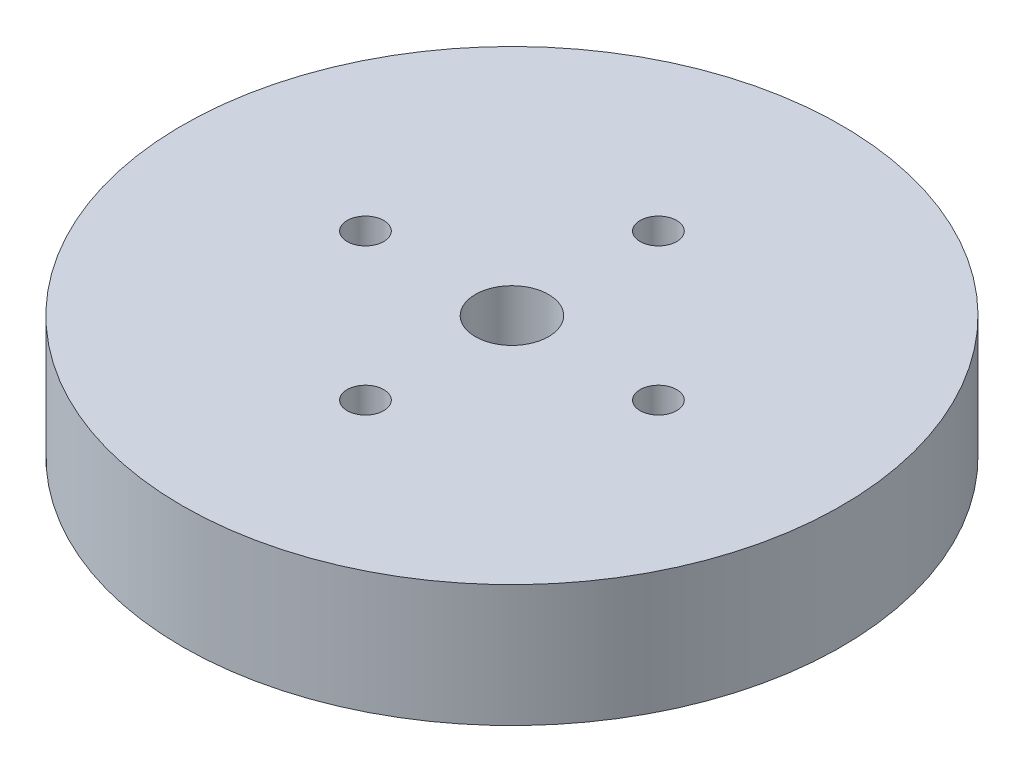
SolidWorks part; units mm, degrees
ref_plane "Front Plane" through (0, 0, 0) normal (0, 0, 1) x (1, 0, 0)
ref_plane "Top Plane" through (0, 0, 0) normal (0, 1, 0) x (1, 0, 0)
ref_plane "Right Plane" through (0, 0, 0) normal (1, 0, 0) x (0, 0, -1)
sketch "Sketch1" plane through (0, 0, 0) normal (0, 1, 0) x (1, 0, 0)
  circle A0 centre (0, 0) radius 13.5
  circle A1 centre (0, 0) radius 1.5
  dimension "D1" = 27
  dimension "D2" = 3
extrude "Boss-Extrude2" add sketch "Sketch1" along normal blind 5 contours A1 | A0
sketch "Sketch2" plane through (0, 5, 0) normal (0, 1, 0) x (1, 0, 0)
  circle A0 centre (0, 0) radius 6
  circle A1 centre (6, 0) radius 0.75
  circle A2 centre (0, -6) radius 0.75
  circle A3 centre (-6, 0) radius 0.75
  circle A4 centre (0, 6) radius 0.75
  point P14 (0, 0)
  dimension "D1" = 12
  dimension "D2" = 1.5
  dimension "D3" = 4
extrude "Cut-Extrude1" cut sketch "Sketch2" against normal blind 34 contours A0 A3 | A0 A3 | A0 A4 | A0 A4 | A0 A2 | A0 A2 | A0 A1
